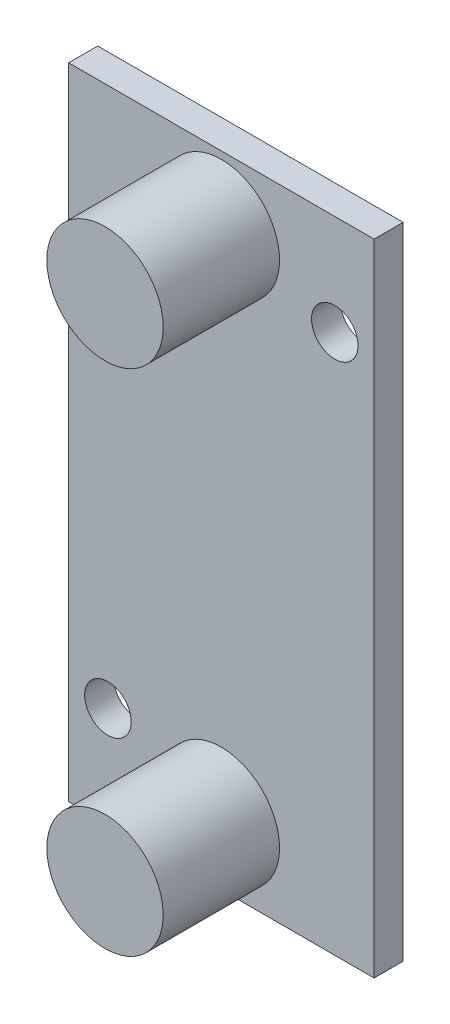
SolidWorks part; units mm, degrees
ref_plane "Front Plane" through (0, 0, 0) normal (0, 0, 1) x (1, 0, 0)
ref_plane "Top Plane" through (0, 0, 0) normal (0, 1, 0) x (1, 0, 0)
ref_plane "Right Plane" through (0, 0, 0) normal (1, 0, 0) x (0, 0, -1)
sketch "Sketch1" plane through (0, 0, 0) normal (0, 0, 1) x (1, 0, 0)
  line L1 (0, 0) -> (21, 0)
  line L2 (0, 0) -> (0, 44)
  line L3 (0, 44) -> (21, 44)
  line L4 (21, 0) -> (21, 44)
  dimension "D1" = 21
  dimension "D2" = 44
extrude "Boss-Extrude1" add sketch "Sketch1" along normal blind 2
sketch "Sketch2" plane through (0, 0, 2) normal (0, 0, 1) x (1, 0, 0)
  line L0 (10.5, 44) -> (10.5, 0) construction
  line L1 (21, 44) -> (0, 44) construction
  line L2 (0, 0) -> (21, 0) construction
  line L3 (21, 0) -> (21, 44) construction
  line L4 (0, 44) -> (0, 0) construction
  circle A0 centre (18.3, 37.1) radius 1.6
  circle A1 centre (2.7, 6.9) radius 1.6
  point P12 (0, 0)
  dimension "D2" = 3.2
  dimension "D4" = 3.2
  dimension "D1" = 2.7
  dimension "D3" = 6.9
  dimension "D5" = 6.9
  dimension "D6" = 2.7
extrude "Cut-Extrude1" cut sketch "Sketch2" against normal through all
sketch "Sketch3" plane through (0, 0, 2) normal (0, 0, 1) x (1, 0, 0)
  line L0 (10.5, 44) -> (10.5, 0) construction
  line L1 (21, 44) -> (0, 44) construction
  line L2 (0, 0) -> (21, 0) construction
  line L3 (0, 22) -> (21, 22) construction
  line L4 (0, 44) -> (0, 0) construction
  line L5 (21, 0) -> (21, 44) construction
  circle A0 centre (10.5, 39.5) radius 4
  circle A1 centre (10.5, 4.5) radius 4
  dimension "D1" = 8
  dimension "D2" = 4.5
extrude "Boss-Extrude2" add sketch "Sketch3" along normal blind 8
